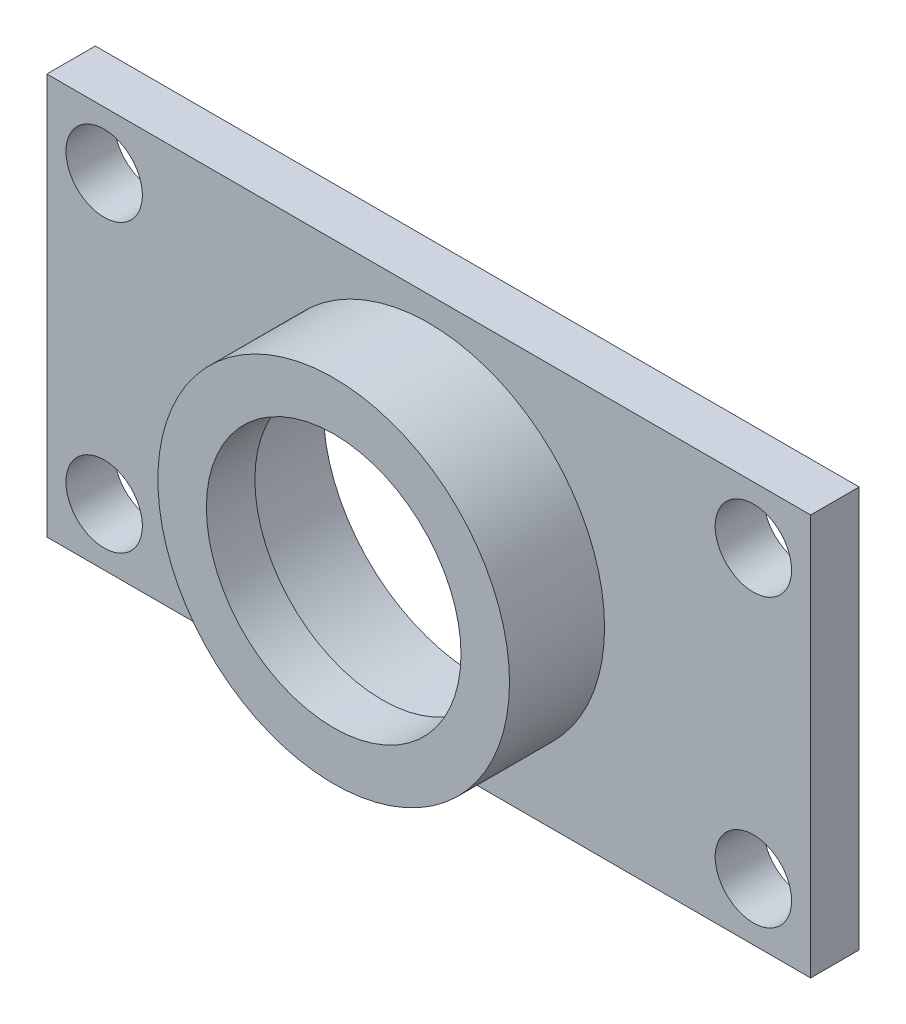
SolidWorks part; units mm, degrees
ref_plane "Front Plane" through (0, 0, 0) normal (0, 0, 1) x (1, 0, 0)
ref_plane "Top Plane" through (0, 0, 0) normal (0, 1, 0) x (1, 0, 0)
ref_plane "Right Plane" through (0, 0, 0) normal (1, 0, 0) x (0, 0, -1)
sketch "Sketch2" plane through (0, 0, 0) normal (0, 0, 1) x (1, 0, 0)
  line L1 (0, 0) -> (40, 0)
  line L2 (0, 0) -> (0, 21)
  line L3 (0, 21) -> (40, 21)
  line L4 (40, 0) -> (40, 21)
  dimension "D1" = 21
  dimension "D2" = 40
extrude "Boss-Extrude1" add sketch "Sketch2" along normal blind 2.54
sketch "Sketch4" plane through (0, 0, 2.54) normal (0, 0, 1) x (1, 0, 0)
  line L0 (0, 21) -> (0, 0) construction
  line L1 (0, 0) -> (40, 0) construction
  circle A0 centre (20, 10.5) radius 9.2075
  dimension "D1" = 18.415
  dimension "D2" = 20
  dimension "D3" = 10.5
extrude "Boss-Extrude2" add sketch "Sketch4" along normal blind 4.9784 contours A0
sketch "Sketch7" plane through (0, 0, 0) normal (0, 0, 1) x (1, 0, 0)
  circle A0 centre (20, 10.5) radius 6.6675
  dimension "D1" = 13.335
extrude "Cut-Extrude2" cut sketch "Sketch7" against normal blind 2.54 from surface at 7.5184 contours A0 starting at face at (29.2075, 10.5, 7.5184)
sketch "Sketch8" plane through (0, 0, 2.54) normal (0, 0, 1) x (1, 0, 0)
  line L0 (40, 0) -> (40, 21) construction
  line L1 (40, 21) -> (0, 21) construction
  line L2 (20, 26.3891) -> (20, -8.0602) construction
  line L3 (0, 21) -> (0, 0) construction
  circle A0 centre (37, 18) radius 2
  circle A1 centre (3, 18) radius 2
  dimension "D1" = 4
  dimension "D2" = 3
  dimension "D3" = 3
  dimension "D4" = 20
extrude "Cut-Extrude3" cut sketch "Sketch8" against normal through all
sketch "Sketch10" plane through (0, 0, 2.54) normal (0, 0, 1) x (1, 0, 0)
  line L0 (0, 0) -> (40, 0) construction
  line L1 (40, 0) -> (40, 21) construction
  line L2 (20, 26.4528) -> (20, -7.1687) construction
  line L3 (0, 21) -> (0, 0) construction
  circle A0 centre (37, 3) radius 2
  circle A1 centre (3, 3) radius 2
  dimension "D1" = 4
  dimension "D2" = 3
  dimension "D3" = 3
  dimension "D4" = 20
extrude "Cut-Extrude4" cut sketch "Sketch10" against normal through all
sketch "Sketch13" plane through (0, 0, 0) normal (0, 0, -1) x (-1, 0, 0)
  line L0 (0, 0) -> (-40, 0) construction
  line L1 (-40, 0) -> (-40, 21) construction
  circle A0 centre (-20, 10.5) radius 8.0645
  dimension "D1" = 16.129
  dimension "D2" = 10.5
  dimension "D3" = 20
extrude "Cut-Extrude5" cut sketch "Sketch13" against normal blind 4.9784
